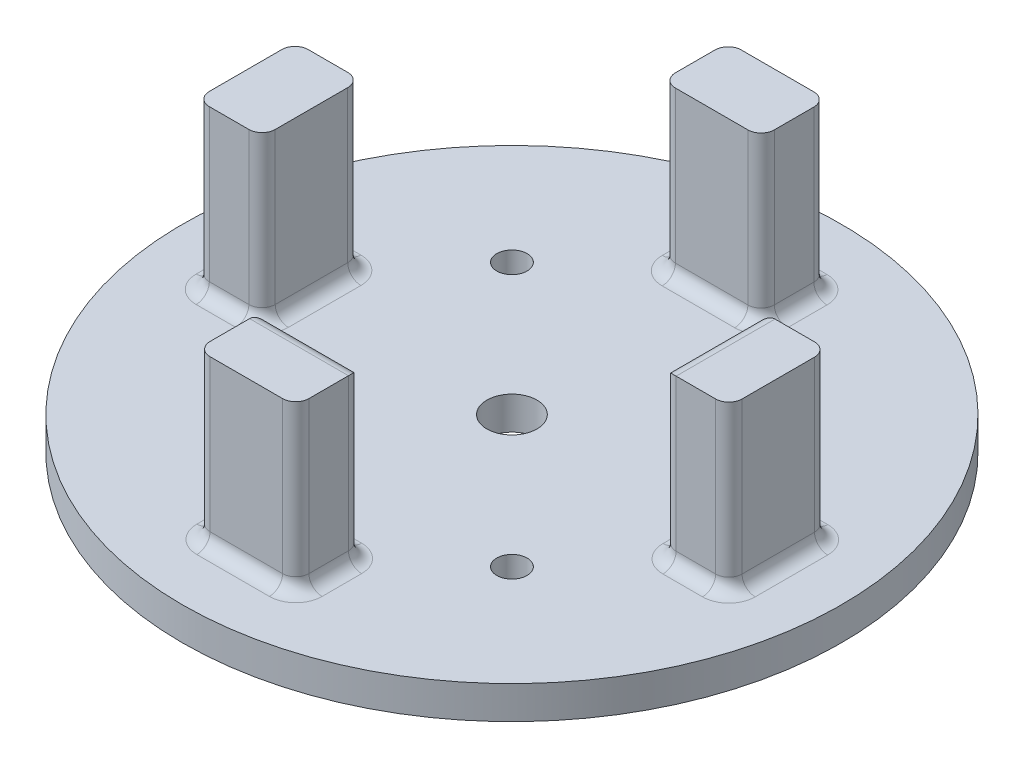
SolidWorks part; units mm, degrees
ref_plane "Front Plane" through (0, 0, 0) normal (0, 0, 1) x (1, 0, 0)
ref_plane "Top Plane" through (0, 0, 0) normal (0, 1, 0) x (1, 0, 0)
ref_plane "Right Plane" through (0, 0, 0) normal (1, 0, 0) x (0, 0, -1)
sketch "Sketch2" plane through (0, 0, 0) normal (0, 1, 0) x (1, 0, 0)
  line L1 (-25.4, 25.4) -> (25.4, 25.4) construction
  line L2 (-25.4, 25.4) -> (-25.4, -25.4) construction
  line L3 (-25.4, -25.4) -> (25.4, -25.4) construction
  line L4 (25.4, 25.4) -> (25.4, -25.4) construction
  line L5 (-25.4, 25.4) -> (25.4, -25.4) construction
  line L6 (-25.4, -25.4) -> (25.4, 25.4) construction
  circle A0 centre (0, 0) radius 63.5
  circle A1 centre (-25.4, 25.4) radius 2.921
  circle A2 centre (25.4, 25.4) radius 2.921
  circle A3 centre (25.4, -25.4) radius 2.921
  circle A4 centre (-25.4, -25.4) radius 2.921
  circle A5 centre (0, 0) radius 4.826
  dimension "D1" = 127
  dimension "D3" = 5.842
  dimension "D4" = 9.652
  dimension "D2" = 50.8
extrude "Boss-Extrude2" add sketch "Sketch2" along normal blind 6.35
sketch "Sketch3" plane through (0, 6.35, 0) normal (0, 1, 0) x (1, 0, 0)
  line L0 (-55, 0) -> (55, 0) construction
  line L1 (-44.9715, 44.831) -> (44.9715, 44.831) construction
  line L2 (-44.9715, 44.831) -> (-44.9715, -44.831) construction
  line L3 (-44.9715, -44.831) -> (44.9715, -44.831) construction
  line L4 (44.9715, 44.831) -> (44.9715, -44.831) construction
  line L5 (-44.9715, 44.831) -> (44.9715, -44.831) construction
  line L6 (-44.9715, -44.831) -> (44.9715, 44.831) construction
  line L7 (-9.525, 38.481) -> (9.525, 38.481)
  line L8 (-9.525, 38.481) -> (-9.525, 51.181)
  line L9 (-9.525, 51.181) -> (9.525, 51.181)
  line L10 (9.525, 38.481) -> (9.525, 51.181)
  line L11 (-9.525, 38.481) -> (9.525, 51.181) construction
  line L12 (-9.525, 51.181) -> (9.525, 38.481) construction
  line L13 (-9.525, -51.181) -> (9.525, -51.181)
  line L14 (9.525, -38.481) -> (9.525, -51.181)
  line L15 (-9.525, -38.481) -> (9.525, -38.481)
  line L16 (-9.525, -38.481) -> (-9.525, -51.181)
  line L17 (-9.525, -51.181) -> (9.525, -38.481) construction
  line L18 (-9.525, -38.481) -> (9.525, -51.181) construction
  line L19 (0, -55) -> (0, 55) construction
  line L20 (-51.3215, 9.525) -> (-38.6215, 9.525)
  line L21 (-51.3215, 9.525) -> (-51.3215, -9.525)
  line L22 (-51.3215, -9.525) -> (-38.6215, -9.525)
  line L23 (-38.6215, 9.525) -> (-38.6215, -9.525)
  line L24 (-51.3215, 9.525) -> (-38.6215, -9.525) construction
  line L25 (-51.3215, -9.525) -> (-38.6215, 9.525) construction
  line L26 (38.6215, 9.525) -> (38.6215, -9.525)
  line L27 (51.3215, -9.525) -> (38.6215, -9.525)
  line L28 (51.3215, 9.525) -> (51.3215, -9.525)
  line L29 (51.3215, 9.525) -> (38.6215, 9.525)
  circle A0 centre (0, 0) radius 63.5 construction
  circle A1 centre (0, 0) radius 63.5 construction
  point P0 (0, 0)
  point P8 (0, 44.831)
  point P19 (0, -44.831)
  point P20 (-44.9715, 0)
  dimension "D1" = 12.7
  dimension "D2" = 19.05
  dimension "D3" = 89.662
extrude "Boss-Extrude3" add sketch "Sketch3" along normal blind 31.75
sketch "Sketch4" plane through (0, 38.1, 0) normal (0, 1, 0) x (1, 0, 0)
  circle A0 centre (0, 0) radius 44.45
  circle A1 centre (0, 0) radius 48.26
  dimension "D1" = 88.9
  dimension "D2" = 3.81
fillet "Fillet1" radius 2.54 34 edges at (51.3215, 6.35, 0) (44.9715, 6.35, -9.525) (44.9715, 6.35, 9.525) (38.6215, 22.225, -9.525) (38.6215, 38.1, 0) (38.6215, 22.225, 9.525) (38.6215, 6.35, 0) (51.3215, 22.225, 9.525) (51.3215, 22.225, -9.525) (-51.3215, 22.225, -9.525) (-51.3215, 22.225, 9.525) (-38.6215, 22.225, 9.525) (-38.6215, 22.225, -9.525) (9.525, 22.225, 51.181) (9.525, 22.225, 38.481) (-9.525, 22.225, 38.481) (-9.525, 22.225, 51.181) (9.525, 22.225, -38.481) (-9.525, 22.225, -38.481) (9.525, 22.225, -51.181) (-9.525, 22.225, -51.181) (0, 6.35, 51.181) (-44.9715, 6.35, 9.525) (0, 6.35, -38.481) (9.525, 6.35, 44.831) (-9.525, 6.35, 44.831) (-38.6215, 6.35, 0) (-51.3215, 6.35, 0) (9.525, 6.35, -44.831) (-9.525, 6.35, -44.831) (0, 38.1, 38.481) (0, 6.35, 38.481) (-44.9715, 6.35, -9.525) (0, 6.35, -51.181)
